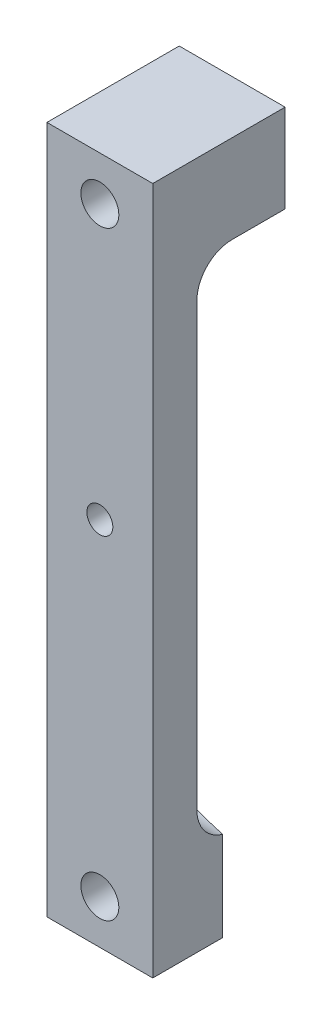
SolidWorks part; units mm, degrees
ref_plane "Front" through (0, 0, 0) normal (0, 0, 1) x (1, 0, 0)
ref_plane "Top" through (0, 0, 0) normal (0, 1, 0) x (1, 0, 0)
ref_plane "Right" through (0, 0, 0) normal (1, 0, 0) x (0, 0, -1)
sketch "Sketch1" plane through (0, 0, 0) normal (0, 0, 1) x (1, 0, 0)
  line L0 (0, 39) -> (0, -39)
  line L1 (0, -39) -> (12, -39)
  line L2 (12, -39) -> (12, 0)
  line L3 (12, 39) -> (0, 39)
  line L4 (-6.7379, 0) -> (17.2192, 0) construction
  line L9 (12, 0) -> (12, 39)
  dimension "D1" = 78
  dimension "D2" = 12
extrude "Extrude1" add sketch "Sketch1" along normal blind 5
sketch "Sketch3" plane through (0, 0, 5) normal (0, 0, 1) x (1, 0, 0)
  line L0 (12, 39) -> (0, 39) construction
  line L1 (0, 39) -> (0, -39) construction
  circle A0 centre (6, 3) radius 1.4732
  dimension "D1" = 2.9464
  dimension "D2" = 6
  dimension "D3" = 36
extrude "Cut-Extrude2" cut sketch "Sketch3" against normal through all
sketch "Sketch4" plane through (0, 0, 0) normal (0, 0, -1) x (-1, 0, 0)
  line L0 (-12, -39) -> (-12, 39) construction
  line L1 (0, 39) -> (-12, 39)
  line L2 (0, 39) -> (0, 29)
  line L3 (0, 29) -> (-12, 29)
  line L4 (-12, 39) -> (-12, 29)
  line L6 (0, -39) -> (-12, -39)
  line L7 (0, -39) -> (0, -29)
  line L8 (0, -29) -> (-12, -29)
  line L9 (-12, -39) -> (-12, -29)
  dimension "D1" = 10
  dimension "D2" = 10
extrude "Extrude2" add sketch "Sketch4" along normal blind 10
fillet "Fillet1" radius 4 2 edges at (6, -29, 0)
sketch "Sketch5" plane through (0, 0, 0) normal (0, 1, 0) x (1, 0, 0)
  line L0 (0, 10) -> (0, 6.192)
  line L2 (12, -5) -> (12, 10) construction
  line L3 (0, 10) -> (12, 10)
  line L4 (12, 8.7846) -> (12, 10)
  line L5 (0, -5) -> (0, 10) construction
  line L6 (0, 6.192) -> (12, 2.9317)
  line L7 (12, 2.9317) -> (12, 8.7846)
  dimension "D1" = 15.2
  dimension "D2" = 3.808
extrude "Cut-Extrude3" cut sketch "Sketch5" against normal up to surface (39 mm away) up to face at (6, -39, -2.5)
hole_wizard "#8 Clearance Hole1" positions "3DSketch1" profile "Sketch7" hole size "#8" standard "Ansi Inch" end condition through all
sketch3d "3DSketch1"
  line L0 (0, 39, 5) -> (0, -39, 5) construction
  line L1 (12, 39, 5) -> (0, 39, 5) construction
  line L2 (0, -39, 5) -> (12, -39, 5) construction
  point P0 (6, 34, 5)
  point P1 (6, -34, 5)
  dimension "D1" = 5
  dimension "D2" = 6
  dimension "D3" = 5
sketch "Sketch7" plane through (6, 34, 5) normal (1, 0, 0) x (0, -1, 0)
  line L0 (0, 0) -> (0, 15)
  line L1 (0, 15) -> (2.1526, 15)
  line L2 (2.1526, 15) -> (2.1526, 0)
  line L5 (2.1526, 0) -> (0, 0)
  line L11 (0, -6.35) -> (0, 107.95) construction
  dimension "Thru Hole Dia." = 4.3053
  dimension "Thru Hole Depth" = 15
